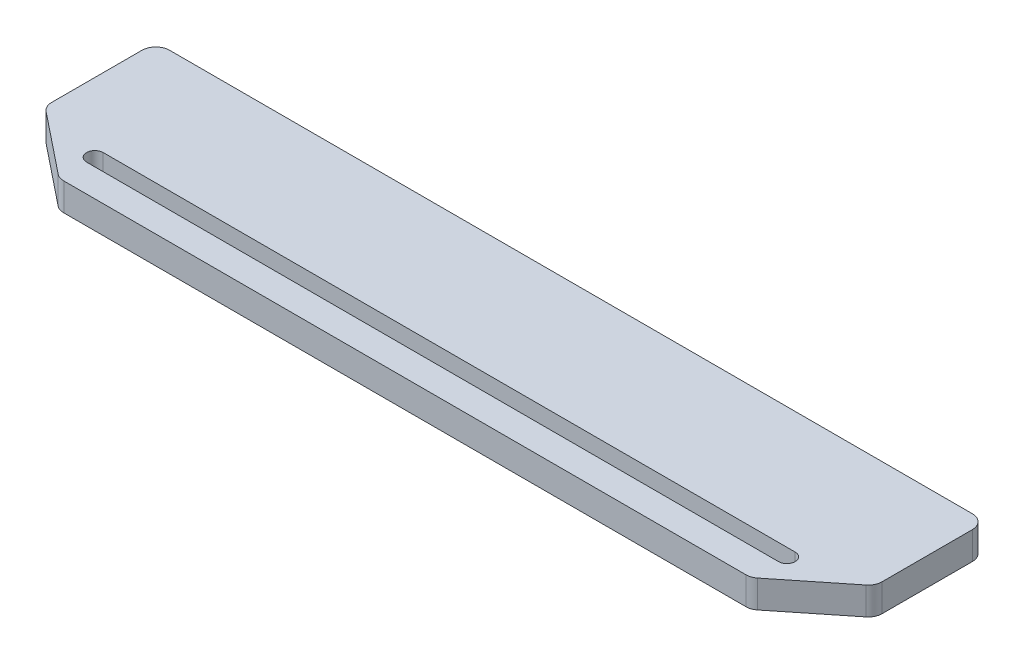
SolidWorks part; units mm, degrees
material "6061 Alloy"
ref_plane "Front Plane" through (0, 0, 0) normal (0, 0, 1) x (1, 0, 0)
ref_plane "Top Plane" through (0, 0, 0) normal (0, 1, 0) x (1, 0, 0)
ref_plane "Right Plane" through (0, 0, 0) normal (1, 0, 0) x (0, 0, -1)
sketch "Sketch1" plane through (0, 0, 0) normal (0, 1, 0) x (1, 0, 0)
  line L0 (0, -5) -> (0, -37.5969)
  line L3 (5, 0) -> (295, 0)
  line L5 (300, -5) -> (300, -37.5969)
  line L6 (1.8765, -41.5012) -> (23.6304, -58.9043)
  line L7 (26.7539, -60) -> (273.2461, -60)
  line L8 (276.3696, -58.9043) -> (298.1235, -41.5012)
  arc A0 (300, -5) -> (295, 0) centre (295, -5) ccw
  arc A1 (0, -5) -> (5, 0) centre (5, -5) cw
  arc A2 (23.6304, -58.9043) -> (26.7539, -60) centre (26.7539, -55) ccw
  arc A3 (276.3696, -58.9043) -> (273.2461, -60) centre (273.2461, -55) cw
  arc A4 (300, -37.5969) -> (298.1235, -41.5012) centre (295, -37.5969) cw
  arc A5 (1.8765, -41.5012) -> (0, -37.5969) centre (5, -37.5969) cw
  point P0 (0, 0)
  point P2 (150, 0)
  point P6 (150, -60)
  point P12 (300, 0)
  point P15 (0, 0)
  point P18 (25, -60)
  point P21 (275, -60)
  point P24 (300, -40)
  point P28 (0, -40)
  dimension "D5" = 5
  dimension "D6" = 5
  dimension "D1" = 300
  dimension "D2" = 250
  dimension "D3" = 40
  dimension "D4" = 20
extrude "Boss-Extrude1" add sketch "Sketch1" along normal blind 10
sketch "Sketch2" plane through (0, 0, 0) normal (0, 1, 0) x (1, 0, 0)
  line L0 (26.7539, -60) -> (273.2461, -60) construction
  line L1 (25, -47) -> (275, -47) construction
  line L2 (25, -44) -> (275, -44)
  line L3 (25, -50) -> (275, -50)
  line L6 (5, 0) -> (295, 0) construction
  line L7 (150, 0) -> (150, -60.0142) construction
  arc A0 (25, -44) -> (25, -50) centre (25, -47) ccw
  arc A1 (275, -50) -> (275, -44) centre (275, -47) ccw
  point P6 (150, -47)
  dimension "D1" = 6
  dimension "D2" = 250
  dimension "D3" = 10
extrude "Cut-Extrude4" cut sketch "Sketch2" against normal through all and the other way through all
